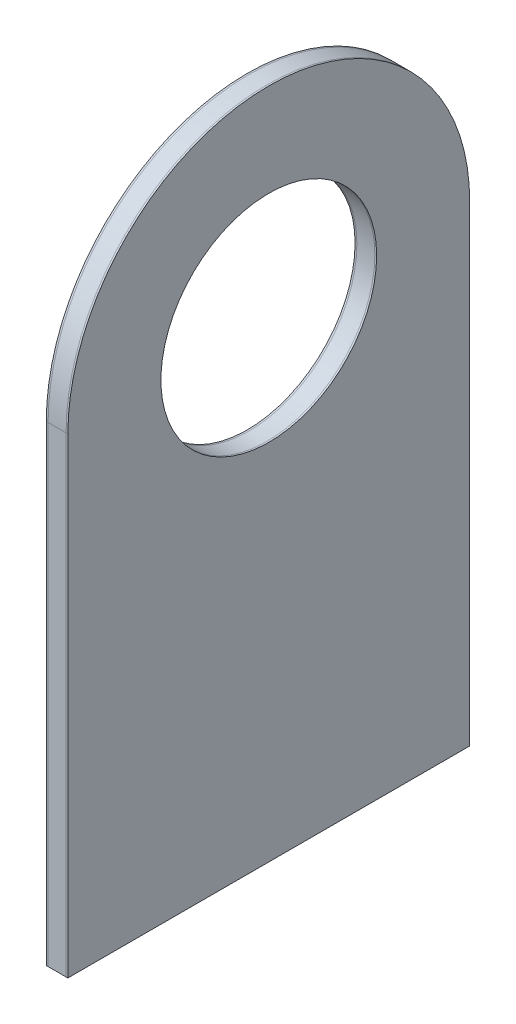
SolidWorks part; units mm, degrees
ref_plane "Front Plane" through (0, 0, 0) normal (0, 0, 1) x (1, 0, 0)
ref_plane "Top Plane" through (0, 0, 0) normal (0, 1, 0) x (1, 0, 0)
ref_plane "Right Plane" through (0, 0, 0) normal (1, 0, 0) x (0, 0, -1)
sketch "Sketch1" plane through (0, 0, 0) normal (1, 0, 0) x (0, 0, -1)
  line L0 (-27.94, 65.532) -> (-27.94, 0)
  line L1 (-27.94, 0) -> (27.94, 0)
  line L2 (27.94, 0) -> (27.94, 65.532)
  circle A0 centre (0, 65.532) radius 15
  arc A1 (27.94, 65.532) -> (-27.94, 65.532) centre (0, 65.532) ccw
  dimension "D1" = 30
  dimension "D2" = 55.88
  dimension "D3" = 65.532
extrude "Boss-Extrude1" add sketch "Sketch1" along normal blind 0.25
sketch "Sketch2" plane through (0.25, 0, 0) normal (1, 0, 0) x (0, 0, -1)
  circle A1 centre (0, 65.532) radius 15
  circle A2 centre (0, 65.532) radius 15
  arc M2 (27.94, 65.532) -> (-27.94, 65.532) centre (0, 65.532) ccw
  line M3 (-27.94, 65.532) -> (-27.94, 0)
  line M4 (-27.94, 0) -> (27.94, 0)
  line M5 (27.94, 0) -> (27.94, 65.532)
  circle M6 centre (0, 65.532) radius 15
  dimension "D1" = 0
extrude "Boss-Extrude2" add sketch "Sketch2" along normal blind 2.5 separate body contours M5 M2 M3 M4 M6
sketch "Sketch3" plane through (2.75, 0, 0) normal (1, 0, 0) x (0, 0, -1)
  circle A1 centre (0, 65.532) radius 15
  circle A2 centre (0, 65.532) radius 15
  circle M2 centre (0, 65.532) radius 15
  line M3 (27.94, 0) -> (27.94, 65.532)
  arc M4 (27.94, 65.532) -> (-27.94, 65.532) centre (0, 65.532) ccw
  line M5 (-27.94, 65.532) -> (-27.94, 0)
  line M6 (-27.94, 0) -> (27.94, 0)
  dimension "D1" = 0
extrude "Boss-Extrude3" add sketch "Sketch3" along normal blind 0.25 separate body contours M6 M3 M4 M5 M2
